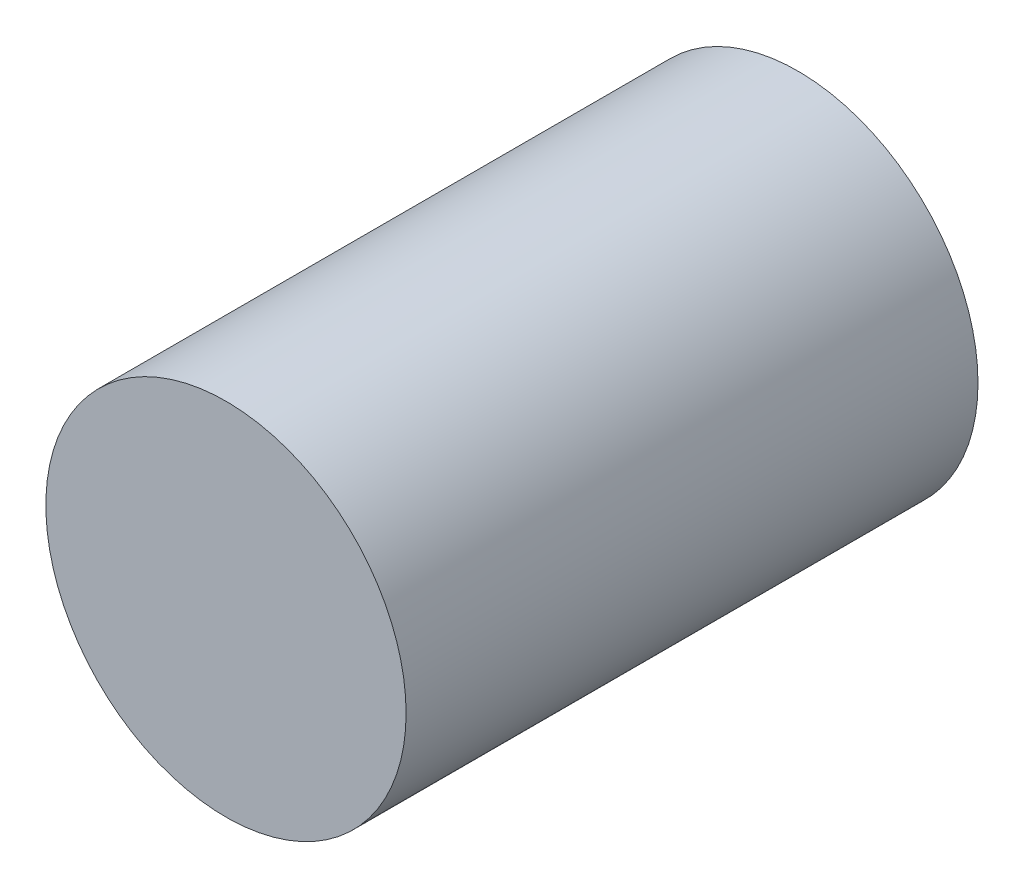
SolidWorks part; units mm, degrees
ref_plane "Front" through (0, 0, 0) normal (0, 0, 1) x (1, 0, 0)
ref_plane "Top" through (0, 0, 0) normal (0, 1, 0) x (1, 0, 0)
ref_plane "Right" through (0, 0, 0) normal (1, 0, 0) x (0, 0, -1)
sketch "Sketch1" plane through (0, 0, 0) normal (0, 0, 1) x (1, 0, 0)
  circle A0 centre (0, 0) radius 1
  dimension "D1" = 2
extrude "Boss-Extrude1" add sketch "Sketch1" along normal blind 3.175
